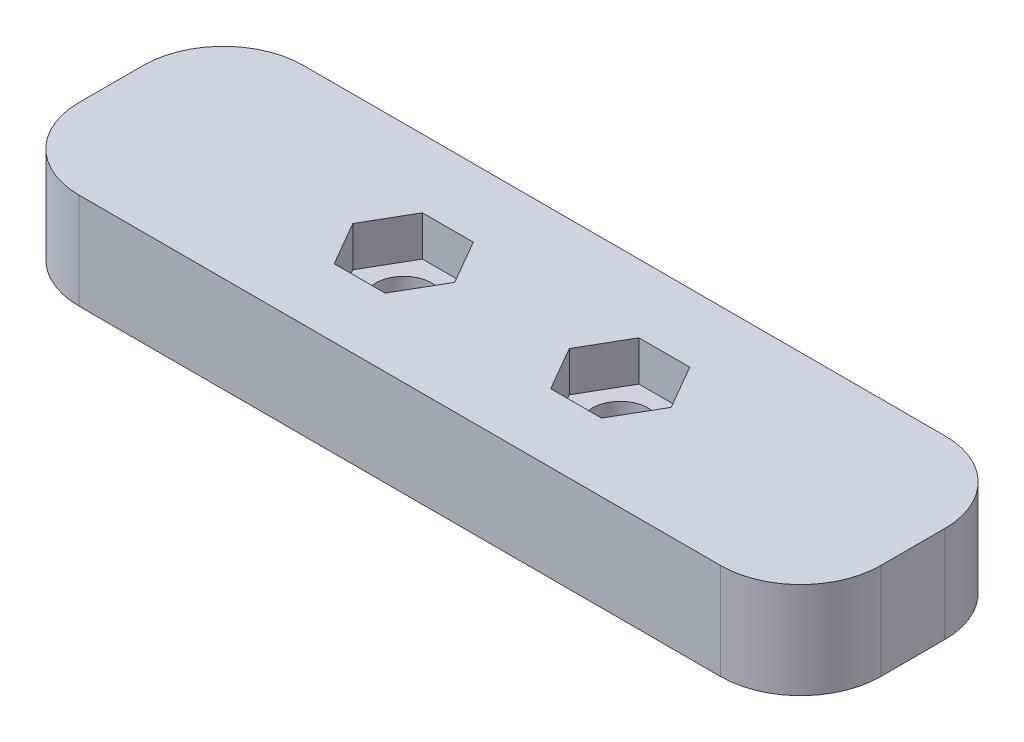
SolidWorks part; units mm, degrees
ref_plane "Front Plane" through (0, 0, 0) normal (0, 0, 1) x (1, 0, 0)
ref_plane "Top Plane" through (0, 0, 0) normal (0, 1, 0) x (1, 0, 0)
ref_plane "Right Plane" through (0, 0, 0) normal (1, 0, 0) x (0, 0, -1)
sketch "Sketch1" plane through (0, 0, 0) normal (0, 1, 0) x (1, 0, 0)
  line L0 (18.25, 7) -> (31.75, 7) construction
  line L1 (5, 0) -> (45, 0)
  line L2 (0, 5) -> (0, 9)
  line L3 (5, 14) -> (45, 14)
  line L4 (50, 5) -> (50, 9)
  circle A0 centre (18.25, 7) radius 1.75
  circle A1 centre (31.75, 7) radius 1.75
  arc A2 (0, 5) -> (5, 0) centre (5, 5) ccw
  arc A3 (50, 5) -> (45, 0) centre (45, 5) cw
  arc A4 (45, 14) -> (50, 9) centre (45, 9) cw
  arc A5 (0, 9) -> (5, 14) centre (5, 9) cw
  point P10 (25, 7)
  point P11 (25, 0)
  point P14 (0, 0)
  point P17 (50, 0)
  point P22 (0, 14)
  dimension "D3" = 3.5
  dimension "D6" = 5
  dimension "D1" = 50
  dimension "D2" = 14
  dimension "D4" = 13.5
  dimension "D5" = 7
extrude "Boss-Extrude1" add sketch "Sketch1" along normal blind 6
sketch "Sketch2" plane through (0, 6, 0) normal (0, 1, 0) x (1, 0, 0)
  line L1 (19.8377, 4.25) -> (21.4254, 7)
  line L2 (21.4254, 7) -> (19.8377, 9.75)
  line L3 (19.8377, 9.75) -> (16.6623, 9.75)
  line L4 (16.6623, 9.75) -> (15.0746, 7)
  line L5 (15.0746, 7) -> (16.6623, 4.25)
  line L6 (16.6623, 4.25) -> (19.8377, 4.25)
  line L7 (33.3377, 4.25) -> (34.9254, 7)
  line L8 (34.9254, 7) -> (33.3377, 9.75)
  line L9 (33.3377, 9.75) -> (30.1623, 9.75)
  line L10 (30.1623, 9.75) -> (28.5746, 7)
  line L11 (28.5746, 7) -> (30.1623, 4.25)
  line L12 (30.1623, 4.25) -> (33.3377, 4.25)
  line L13 (5, 0) -> (45, 0) construction
  circle A0 centre (18.25, 7) radius 2.75 construction
  circle A1 centre (31.75, 7) radius 2.75 construction
  dimension "D1" = 5.5
extrude "Cut-Extrude1" cut sketch "Sketch2" against normal blind 2.5
